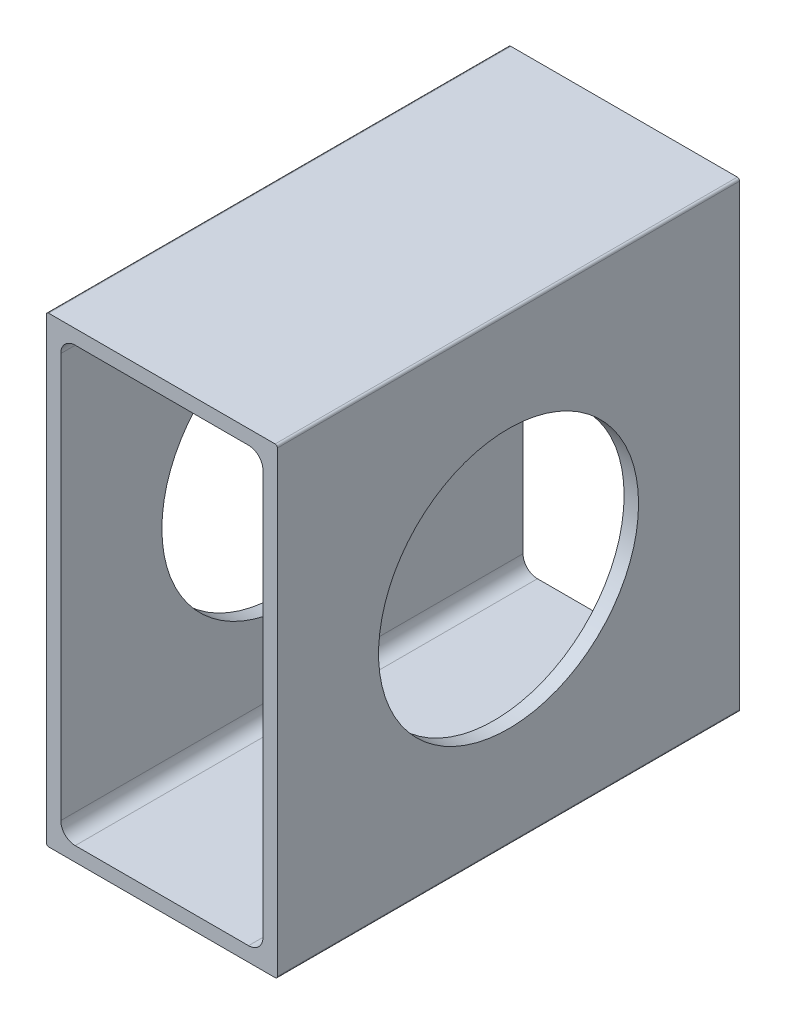
SolidWorks part; units mm, degrees
ref_plane "Front Plane" through (0, 0, 0) normal (0, 0, 1) x (1, 0, 0)
ref_plane "Top Plane" through (0, 0, 0) normal (0, 1, 0) x (1, 0, 0)
ref_plane "Right Plane" through (0, 0, 0) normal (1, 0, 0) x (0, 0, -1)
ref_plane "Plane1" through (0, 0, 0) normal (0, 0, -1) x (-1, 0, 0)
sketch "Sketch1" plane through (0, 0, 0) normal (0, 0, -1) x (-1, 0, 0)
  line L0 (-11.1125, -22.225) -> (-11.1125, 22.225)
  line L1 (-9.525, 23.8125) -> (9.525, 23.8125)
  line L2 (11.1125, 22.225) -> (11.1125, -22.225)
  line L3 (9.525, -23.8125) -> (-9.525, -23.8125)
  line L4 (-12.7, 25.146) -> (-12.7, -25.146)
  line L5 (-12.446, -25.4) -> (12.446, -25.4)
  line L6 (12.7, -25.146) -> (12.7, 25.146)
  line L7 (12.446, 25.4) -> (-12.446, 25.4)
  arc A0 (-11.1125, 22.225) -> (-9.525, 23.8125) centre (-9.525, 22.225) cw
  arc A1 (9.525, 23.8125) -> (11.1125, 22.225) centre (9.525, 22.225) cw
  arc A2 (11.1125, -22.225) -> (9.525, -23.8125) centre (9.525, -22.225) cw
  arc A3 (-9.525, -23.8125) -> (-11.1125, -22.225) centre (-9.525, -22.225) cw
  arc A4 (-12.7, -25.146) -> (-12.446, -25.4) centre (-12.446, -25.146) ccw
  arc A5 (12.446, -25.4) -> (12.7, -25.146) centre (12.446, -25.146) ccw
  arc A6 (12.7, 25.146) -> (12.446, 25.4) centre (12.446, 25.146) ccw
  arc A7 (-12.446, 25.4) -> (-12.7, 25.146) centre (-12.446, 25.146) ccw
extrude "Boss-Extrude1" add sketch "Sketch1" against normal blind 50.8
sketch "Sketch2" plane through (-12.7, 0, 0) normal (-1, 0, 0) x (0, 0, 1)
  line L0 (0, 0) -> (25.4, 0) construction
  circle A0 centre (25.4, 0) radius 14.2875
  dimension "D1" = 28.575
  dimension "D2" = 25.4
extrude "Cut-Extrude1" cut sketch "Sketch2" against normal blind 50.8
